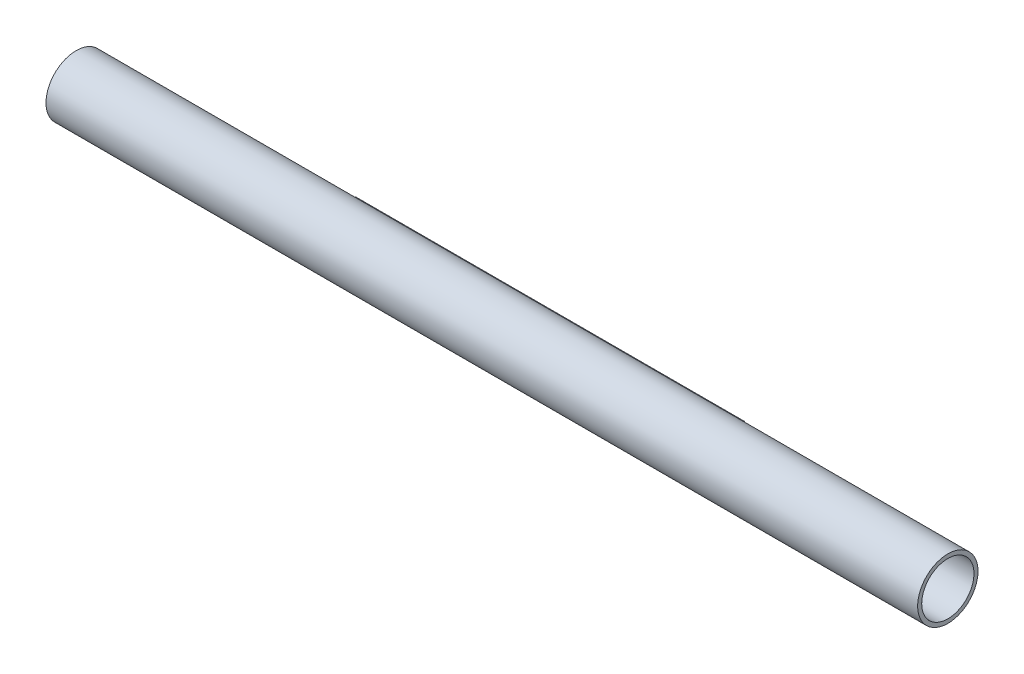
SolidWorks part; units mm, degrees
ref_plane "Front Plane" through (0, 0, 0) normal (0, 0, 1) x (1, 0, 0)
ref_plane "Top Plane" through (0, 0, 0) normal (0, 1, 0) x (1, 0, 0)
ref_plane "Right Plane" through (0, 0, 0) normal (1, 0, 0) x (0, 0, -1)
sketch "Sketch1" plane through (0, 0, 0) normal (1, 0, 0) x (0, 0, -1)
  line L1 (27.94, -6.35) -> (48.26, -6.35)
  line L2 (27.94, -6.35) -> (27.94, 6.35)
  line L3 (27.94, 6.35) -> (48.26, 6.35)
  line L4 (48.26, -6.35) -> (48.26, 6.35)
  line L5 (27.94, -6.35) -> (48.26, 6.35) construction
  line L6 (27.94, 6.35) -> (48.26, -6.35) construction
  circle A0 centre (0, 0) radius 38.1
  point P3 (38.1, 0)
  dimension "D1" = 76.2
  dimension "D2" = 20.32
  dimension "D3" = 12.7
extrude "Boss-Extrude1" add sketch "Sketch1" against normal blind 491.49 contours L3 A0 L1 L2 | A0 L1 L4 L3 | L1 A0 L3 L2
sketch "Sketch2" plane through (0, 0, 0) normal (1, 0, 0) x (0, 0, -1)
  circle A0 centre (0, 0) radius 38.1
  point P0 (0, 0)
extrude "Boss-Extrude2" add sketch "Sketch2" along normal blind 304.8
sketch "Sketch3" plane through (-491.49, 0, 0) normal (-1, 0, 0) x (0, 0, 1)
  circle A0 centre (0, 0) radius 38.1
extrude "Boss-Extrude3" add sketch "Sketch3" along normal blind 304.8
sketch "Sketch4" plane through (-796.29, 0, 0) normal (-1, 0, 0) x (0, 0, 1)
  circle A2 centre (0, 0) radius 33.02
  circle A3 centre (0, 0) radius 33.02
  dimension "D1" = 5.08
extrude "Cut-Extrude1" cut sketch "Sketch4" against normal through all
